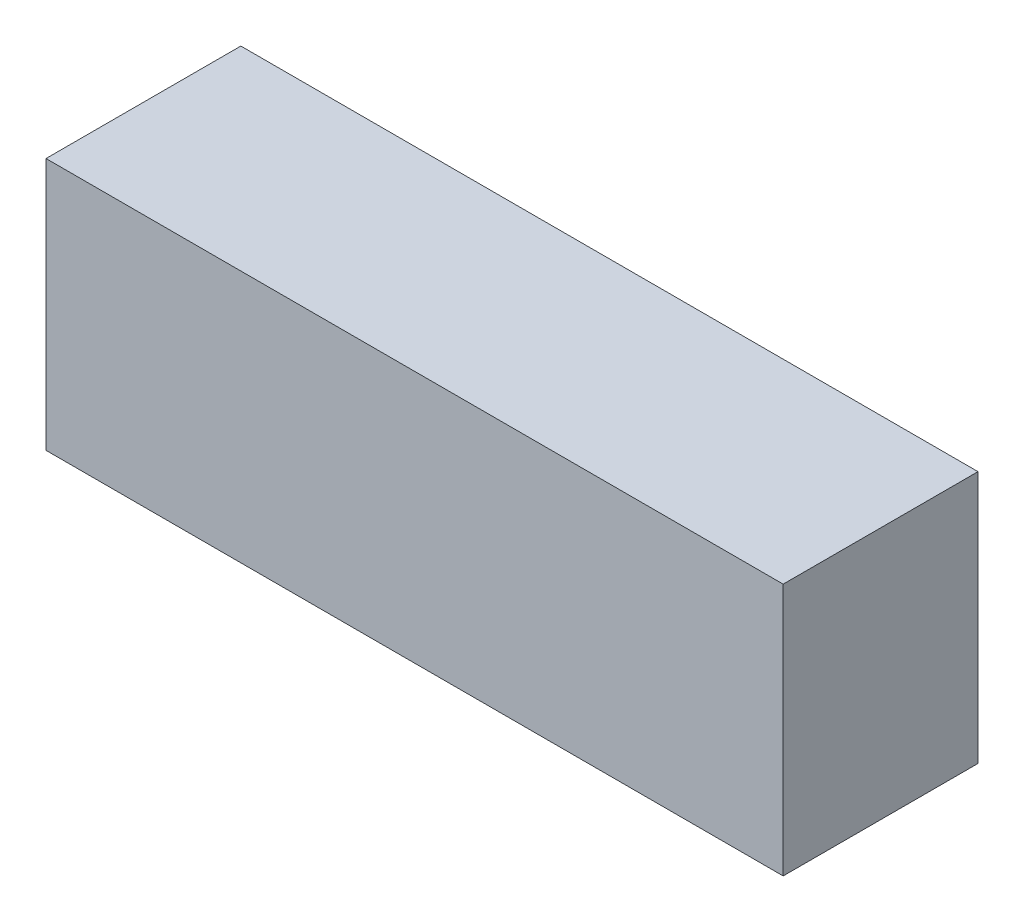
SolidWorks part; units mm, degrees
ref_plane "前视基准面" through (0, 0, 0) normal (0, 0, 1) x (1, 0, 0)
ref_plane "上视基准面" through (0, 0, 0) normal (0, 1, 0) x (1, 0, 0)
ref_plane "右视基准面" through (0, 0, 0) normal (1, 0, 0) x (0, 0, -1)
sketch "草图1" plane through (0, 0, 0) normal (0, 0, 1) x (1, 0, 0)
  line L0 (-37.9132, 0) -> (-37.9132, 24)
  line L1 (-37.9132, 24) -> (32.0868, 24)
  line L2 (32.0868, 24) -> (32.0868, 0)
  line L3 (32.0868, 0) -> (-37.9132, 0)
  dimension "D1" = 24
  dimension "D2" = 70
extrude "凸台-拉伸1" add sketch "草图1" along normal blind 18.5
